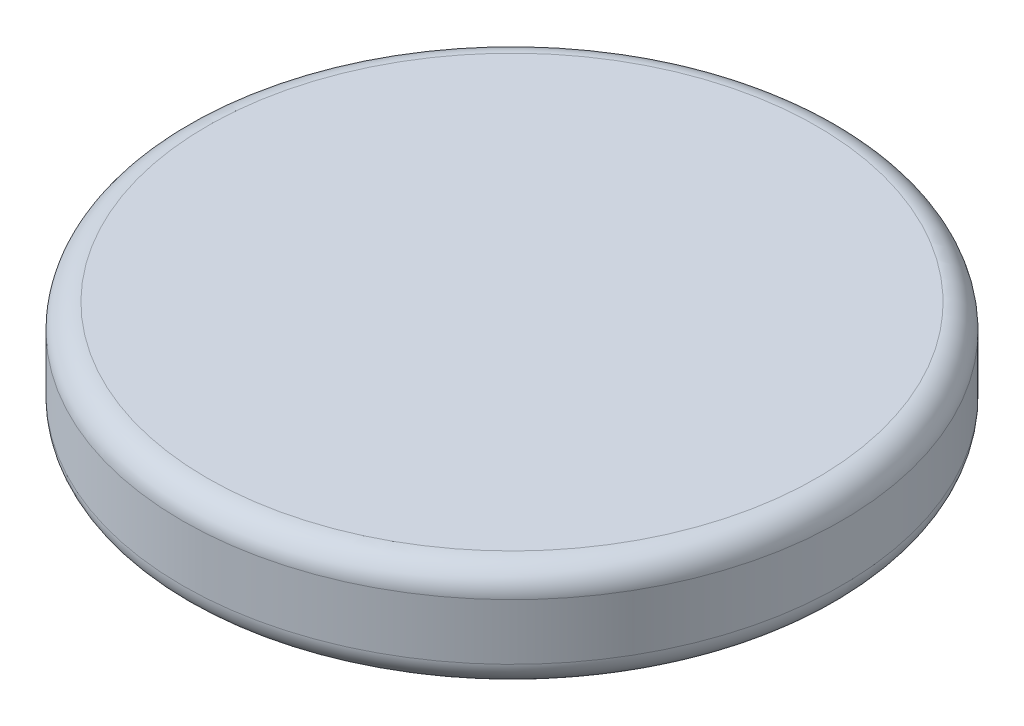
SolidWorks part; units mm, degrees
material "1060 Alloy"
ref_plane "Front Plane" through (0, 0, 0) normal (0, 0, 1) x (1, 0, 0)
ref_plane "Top Plane" through (0, 0, 0) normal (0, 1, 0) x (1, 0, 0)
ref_plane "Right Plane" through (0, 0, 0) normal (1, 0, 0) x (0, 0, -1)
sketch "Sketch2" plane through (0, 0, 0) normal (0, 1, 0) x (1, 0, 0)
  circle A0 centre (0, 0) radius 10
  dimension "D1" = 20
extrude "Boss-Extrude1" add sketch "Sketch2" along normal blind 3.2
fillet "Fillet1" radius 0.75 2 edges at (0, 0, 10) (0, 3.2, 10)
